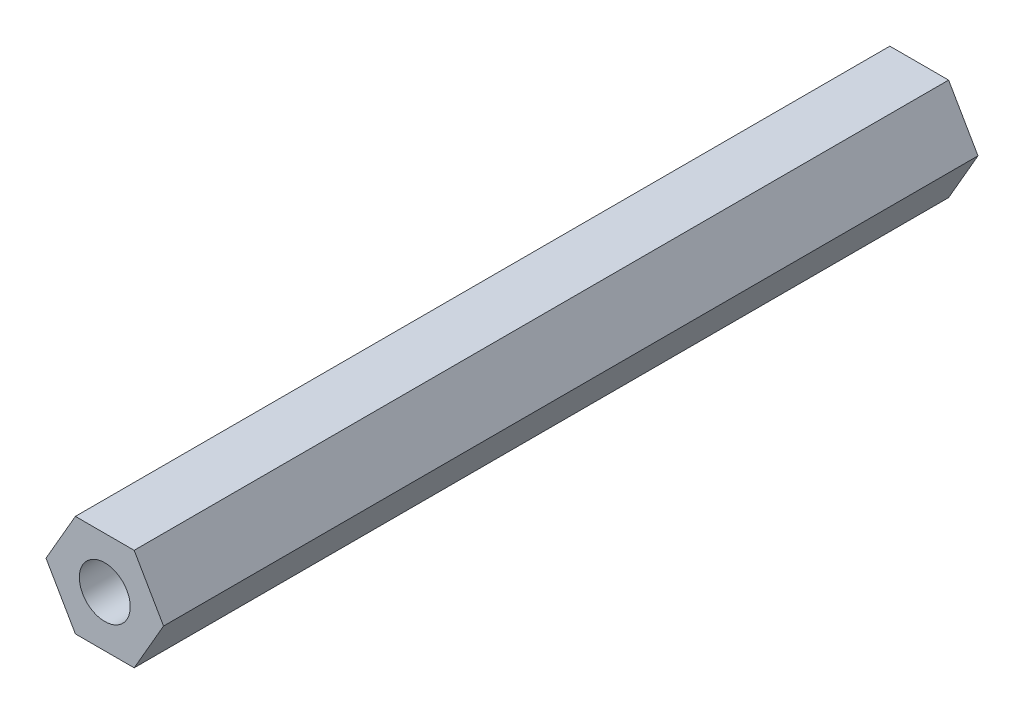
SolidWorks part; units mm, degrees
ref_plane "Front Plane" through (0, 0, 0) normal (0, 0, 1) x (1, 0, 0)
ref_plane "Top Plane" through (0, 0, 0) normal (0, 1, 0) x (1, 0, 0)
ref_plane "Right Plane" through (0, 0, 0) normal (1, 0, 0) x (0, 0, -1)
sketch "Sketch1" plane through (0, 0, 0) normal (0, 0, 1) x (1, 0, 0)
  line L0 (0, 6.35) -> (0, 0)
  line L1 (-7.3323, 0) -> (-3.6662, -6.35)
  line L2 (-3.6662, -6.35) -> (3.6662, -6.35)
  line L3 (3.6662, -6.35) -> (7.3323, 0)
  line L4 (7.3323, 0) -> (3.6662, 6.35)
  line L5 (3.6662, 6.35) -> (-3.6662, 6.35)
  line L6 (-3.6662, 6.35) -> (-7.3323, 0)
  circle A0 centre (0, 0) radius 6.35 construction
  dimension "D1" = 6.35
extrude "Boss-Extrude1" add sketch "Sketch1" along normal offset from surface (514.4834 mm away) 25.4
sketch "Sketch2" plane through (0, 0, 514.4834) normal (0, 0, 1) x (1, 0, 0)
  circle A0 centre (0, 0) radius 3.175
  dimension "D1" = 6.35
extrude "Cut-Extrude1" cut sketch "Sketch2" against normal through all both and the other way through all contours A0
sketch "Sketch3" plane through (0, 0, 0) normal (0, 0, -1) x (-1, 0, 0)
  line L1 (3.6662, -6.35) -> (7.3323, 0)
  line L2 (7.3323, 0) -> (3.6662, 6.35)
  line L3 (3.6662, 6.35) -> (-3.6662, 6.35)
  line L4 (-3.6662, 6.35) -> (-7.3323, 0)
  line L5 (-7.3323, 0) -> (-3.6662, -6.35)
  line L6 (-3.6662, -6.35) -> (3.6662, -6.35)
  circle A0 centre (0, 0) radius 6.35 construction
extrude "Cut-Extrude2" cut sketch "Sketch3" against normal blind 412.8834
